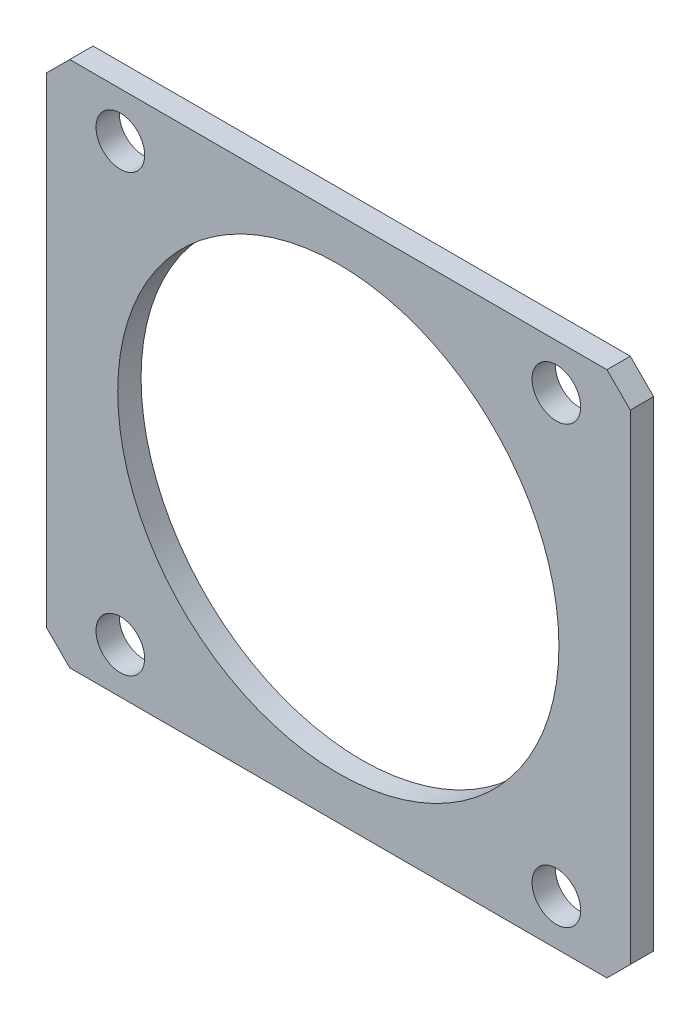
SolidWorks part; units mm, degrees
material "304 SSTL"
ref_plane "Front" through (0, 0, 0) normal (0, 0, 1) x (1, 0, 0)
ref_plane "Top" through (0, 0, 0) normal (0, 1, 0) x (1, 0, 0)
ref_plane "Right" through (0, 0, 0) normal (1, 0, 0) x (0, 0, -1)
sketch "Sketch1" plane through (0, 0, 0) normal (0, 0, 1) x (1, 0, 0)
  line L0 (0, 0) -> (0, 25.781) construction
  line L1 (-28.575, 25.781) -> (28.575, 25.781)
  line L2 (-28.575, 25.781) -> (-28.575, -25.781)
  line L3 (-28.575, -25.781) -> (28.575, -25.781)
  line L4 (28.575, 25.781) -> (28.575, -25.781)
  line L5 (0, 0) -> (28.575, 0) construction
  circle A0 centre (0, 0) radius 21.59
  dimension "D2" = 43.18
  dimension "D1" = 57.15
  dimension "D3" = 51.562
extrude "Boss-Extrude1" add sketch "Sketch1" along normal blind 2.286
hole_wizard "3/16 (0.1875) Diameter Hole1" positions "Sketch3" profile "Sketch2" hole size "3/16" standard "Ansi Inch" end condition through all
sketch "Sketch3" plane through (0, 0, 2.286) normal (0, 0, 1) x (1, 0, 0)
  line L0 (-21.336, 21.336) -> (21.336, 21.336) construction
  line L1 (-21.336, 21.336) -> (-21.336, -21.336) construction
  line L2 (-21.336, -21.336) -> (21.336, -21.336) construction
  line L3 (21.336, -21.336) -> (21.336, 21.336) construction
  line L4 (0, 0) -> (0, 21.336) construction
  line L5 (0, 0) -> (21.336, 0) construction
  point P0 (21.336, 21.336)
  point P1 (-21.336, 21.336)
  point P3 (-21.336, -21.336)
  point P5 (21.336, -21.336)
  dimension "D1" = 42.672
sketch "Sketch2" plane through (21.336, 21.336, 2.286) normal (1, 0, 0) x (0, -1, 0)
  line L0 (0, 0) -> (0, 2.286)
  line L1 (0, 2.286) -> (2.3812, 2.286)
  line L2 (2.3812, 2.286) -> (2.3812, 0)
  line L5 (2.3812, 0) -> (0, 0)
  line L11 (0, -6.35) -> (0, 107.95) construction
  dimension "Thru Hole Dia." = 4.7625
  dimension "Thru Hole Depth" = 2.286
chamfer "Chamfer1" distance 2.286 angle 45 4 edges at (28.575, 25.781, 1.143) (-28.575, 25.781, 1.143) (28.575, -25.781, 1.143) (-28.575, -25.781, 1.143)
